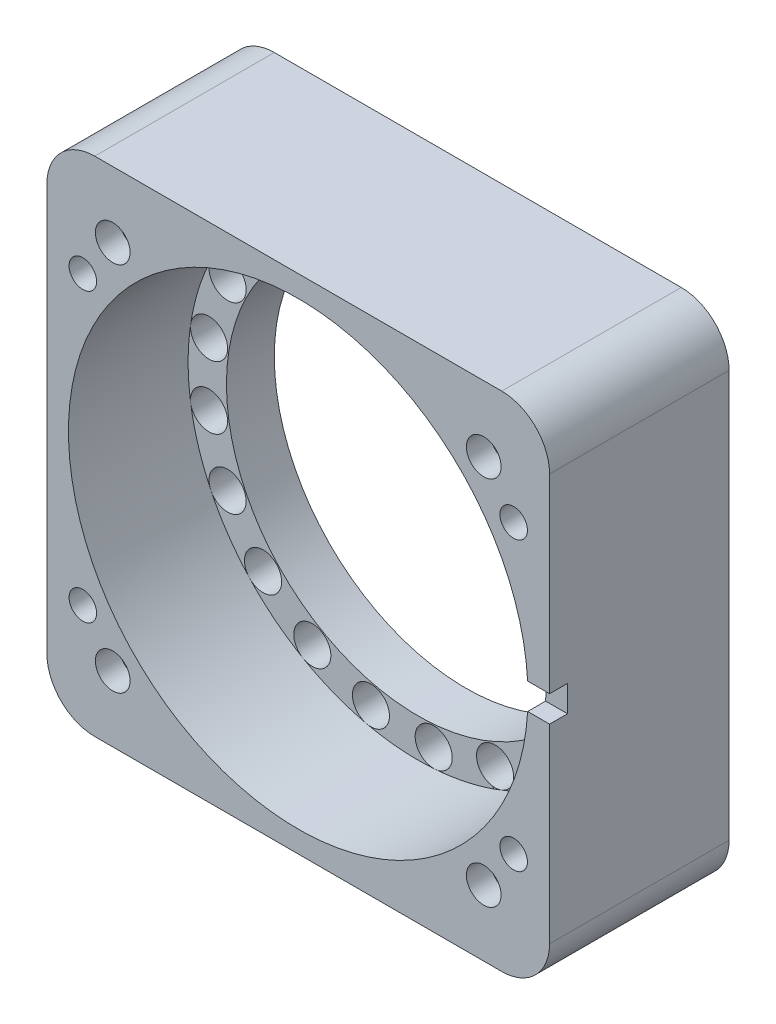
SolidWorks part; units mm, degrees
other "标注1"
sketch "草图9" plane through (-21, -21, 36) normal (-0.2153, -0.0648, 0.9744) x (0.3119, -0.9501, 0.0057)
other "标注2"
sketch "草图20" plane through (-30, -30, 20) normal (-0.0347, -0.0183, 0.9992) x (0.9994, -0.0065, 0.0346)
other "标注3"
sketch "草图27" plane through (-23.5298, 22.2328, 18) normal (-0.0197, 0.0107, 0.9997) x (0.9998, 0.0061, 0.0196)
ref_plane "前视基准面" through (0, 0, 0) normal (0, 0, 1) x (1, 0, 0)
ref_plane "上视基准面" through (0, 0, 0) normal (0, 1, 0) x (1, 0, 0)
ref_plane "右视基准面" through (0, 0, 0) normal (1, 0, 0) x (0, 0, -1)
sketch "草图1" plane through (0, 0, 0) normal (0, 0, 1) x (1, 0, 0)
  line L5 (-17.2128, -17.2128) -> (24.7872, 24.7872) construction
  line L6 (-21, 21) -> (21, -21) construction
  line L7 (21, 21) -> (-21, 21)
  line L8 (21, 21) -> (21, -21)
  line L9 (21, -21) -> (-21, -21)
  line L10 (-21, 21) -> (-21, -21)
  line L11 (0, -21) -> (0, 21) construction
  line L12 (21, 0) -> (-21, 0) construction
  circle A9 centre (0, 0) radius 30 construction
  circle A30 centre (15.5, 15.5) radius 1.55 construction
  circle A31 centre (15.5, -15.5) radius 1.55 construction
  circle A32 centre (-15.5, -15.5) radius 1.55 construction
  circle A33 centre (-15.5, 15.5) radius 1.55 construction
  point P31 (0, 0)
  point P37 (0, 0)
  point P48 (0, 0)
  dimension "D1" = 42
  dimension "D4" = 60
  dimension "D6" = 42
  dimension "D2" = 15.5
  dimension "D3" = 15.5
  dimension "D9" = 3.1
  dimension "D10" = 4
extrude "凸台-拉伸1" add sketch "草图1" along normal blind 15 contours L7 L10 L9 L8 A33 A32 A31 A30
fillet "圆角2" radius 4 4 edges at (21, -21, 7.5) (-21, -21, 7.5) (-21, 21, 7.5) (21, 21, 7.5)
sketch "草图23" plane through (0, 0, 0) normal (0, 0, -1) x (-1, 0, 0)
  line L0 (-21, 17) -> (-21, -17) construction
  line L1 (-21, 13) -> (-17, 13)
  line L2 (-21, 13) -> (-21, 9)
  line L5 (-17, 21) -> (17, 21) construction
  line L18 (-21, 9) -> (-17, 13)
  line L19 (9, 21) -> (13, 17)
  line L20 (13, 21) -> (13, 17)
  line L21 (13, 21) -> (9, 21)
  line L22 (21, -9) -> (17, -13)
  line L23 (21, -13) -> (17, -13)
  line L24 (21, -13) -> (21, -9)
  line L25 (-9, -21) -> (-13, -17)
  line L26 (-13, -21) -> (-13, -17)
  line L27 (-13, -21) -> (-9, -21)
  point P19 (0, 0)
  point P23 (-7, 0)
  dimension "D1" = 4
  dimension "D2" = 4
  dimension "D3" = 8
  dimension "D4" = 4
extrude "切除-拉伸14" [suppressed] cut sketch "草图23" against normal blind 3
sketch "草图24" plane through (0, 0, 15) normal (0, 0, 1) x (1, 0, 0)
  line L0 (-21, 13) -> (-17, 13)
  line L1 (-21, 13) -> (-21, 9)
  line L16 (-21, 17) -> (-21, -17) construction
  line L17 (17, 21) -> (-17, 21) construction
  line L30 (-21, 9) -> (-17, 13)
  line L40 (9, 21) -> (13, 17)
  line L41 (13, 21) -> (13, 17)
  line L42 (13, 21) -> (9, 21)
  line L43 (21, -9) -> (17, -13)
  line L44 (21, -13) -> (17, -13)
  line L45 (21, -13) -> (21, -9)
  line L46 (-9, -21) -> (-13, -17)
  line L47 (-13, -21) -> (-13, -17)
  line L48 (-13, -21) -> (-9, -21)
  point P16 (0.2043, -0.1277)
  point P20 (0.2043, -0.1277)
  point P21 (0, 0)
  point P24 (-7, 0)
  dimension "D1" = 4
  dimension "D2" = 4
  dimension "D3" = 8
  dimension "D4" = 4
extrude "切除-拉伸15" [suppressed] cut sketch "草图24" against normal blind 4
sketch "草图25" plane through (0, 0, 15) normal (0, 0, 1) x (1, 0, 0)
  line L0 (17, 21) -> (-17, 21) construction
  line L1 (-21, 17) -> (-21, -17) construction
  line L2 (0, 22.2328) -> (0, -23.0812) construction
  line L3 (-23.5298, 0) -> (36.1925, 0) construction
  circle A0 centre (-18, 12) radius 1.15
  circle A1 centre (18, 12) radius 1.15
  circle A2 centre (18, -12) radius 1.15
  circle A3 centre (-18, -12) radius 1.15
  dimension "D1" = 2.3
  dimension "D2" = 9
  dimension "D3" = 3
extrude "切除-拉伸16" cut sketch "草图25" against normal through all
sketch "草图28" plane through (0, 0, 15) normal (0, 0, 1) x (1, 0, 0)
  line L0 (-23.5298, 0) -> (36.1925, 0) construction
  line L1 (0, 22.2328) -> (0, -23.0812) construction
  circle A0 centre (-15.5, 15.5) radius 1.45
  circle A1 centre (15.5, 15.5) radius 1.45
  circle A2 centre (15.5, -15.5) radius 1.45
  circle A3 centre (-15.5, -15.5) radius 1.45
  point P15 (0, 0)
  dimension "D1" = 2.9
  dimension "D2" = 15.5
  dimension "D3" = 15.5
  dimension "D4" = 4
extrude "切除-拉伸17" cut sketch "草图28" against normal blind 2
sketch "草图29" plane through (0, 0, 0) normal (0, 0, -1) x (-1, 0, 0)
  line L2 (-16.9706, 16.9706) -> (0, 0) construction
  line L3 (0, 22.2328) -> (0, -23.0812) construction
  circle A0 centre (-16.9706, 16.9706) radius 2.15
  circle A1 centre (16.9706, 16.9706) radius 2.15
  circle A2 centre (16.9706, -16.9706) radius 2.15
  circle A3 centre (-16.9706, -16.9706) radius 2.15
  point P12 (0, 0)
  dimension "D4" = 4.3
  dimension "D1" = 24
  dimension "D3" = 45
  dimension "D2" = 4
extrude "切除-拉伸18" cut sketch "草图29" against normal blind 6
sketch "草图30" plane through (0, 0, 15) normal (0, 0, 1) x (1, 0, 0)
  circle A0 centre (0, 0) radius 19.2
  dimension "D1" = 38.4
extrude "切除-拉伸19" cut sketch "草图30" against normal through all
sketch "草图31" plane through (0, 0, 0) normal (0, 0, -1) x (-1, 0, 0)
  circle A0 centre (0, 0) radius 19.35
  circle A1 centre (0, 0) radius 16
  dimension "D1" = 38.7
  dimension "D2" = 32
extrude "凸台-拉伸2" add sketch "草图31" against normal offset from surface (5 mm away) 10 up to face at (19.2, 0, 15)
sketch "草图32" plane through (0, 0, 5) normal (0, 0, 1) x (1, 0, 0)
  line L1 (-23.5298, 0) -> (36.1925, 0) construction
  circle A0 centre (17.65, 0) radius 1.55
  circle A1 centre (0, 0) radius 19.2 construction
  dimension "D1" = 3.1
extrude "切除-拉伸22" cut sketch "草图32" against normal blind 3
pattern_circular "阵列(圆周)1" count 21 over 360 about axis through (0, 0, 0) along (0, 0, 1) of "切除-拉伸22"
sketch "草图33" plane through (0, 0, 0) normal (0, 0, -1) x (-1, 0, 0)
  circle A0 centre (0, 0) radius 18.75
  dimension "D1" = 37.5
extrude "切除-拉伸23" cut sketch "草图33" against normal blind 1
sketch "草图34" plane through (0, 0, 15) normal (0, 0, 1) x (1, 0, 0)
  line L0 (-23.5298, 0) -> (36.1925, 0) construction
  line L1 (18.2454, 1.1) -> (23.2454, 1.1)
  line L2 (18.2454, 1.1) -> (18.2454, -1.1)
  line L3 (18.2454, -1.1) -> (23.2454, -1.1)
  line L4 (23.2454, 1.1) -> (23.2454, -1.1)
  line L5 (20.7454, -1.1) -> (20.7454, 1.1) construction
  line L6 (18.2454, 0) -> (23.2454, 0) construction
  point P0 (20.7454, 0)
  dimension "D1" = 2.2
  dimension "D2" = 5
extrude "切除-拉伸24" cut sketch "草图34" against normal blind 1.5
equation "\"m\"= 0.6"
equation "\"z\"= 62"
equation "\"a\"= 20"
equation "\"d\"= \"m\" * \"z\""
equation "\"da\"= \"m\" * ( \"z\" - 2 )"
equation "\"df\"= \"d\" + 2.5 * \"m\""
equation "\"db\"= \"d\" * cos ( \"a\" )"
equation "\"s\"= pi * \"m\" / 2"
equation "\"sr\"= 360 / \"z\" / 4"
